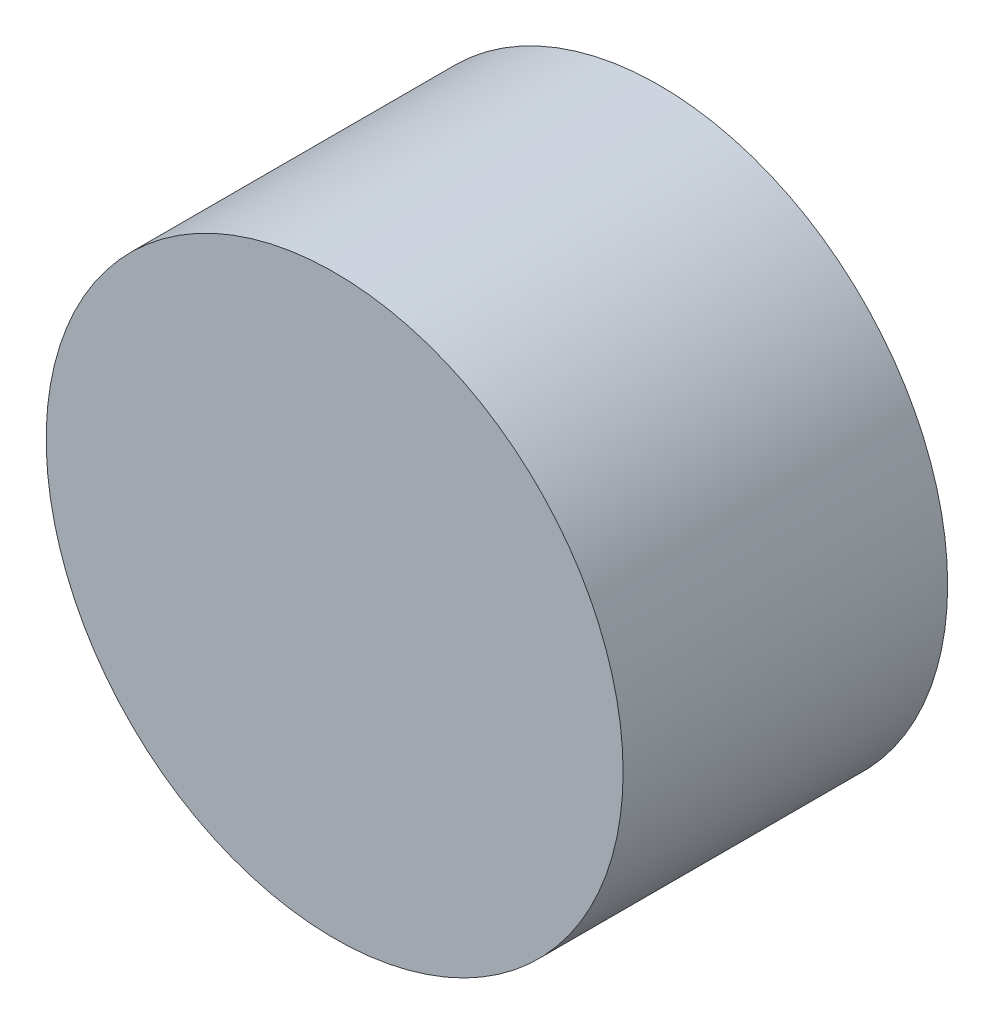
SolidWorks part; units mm, degrees
ref_plane "Płaszczyzna przednia" through (0, 0, 0) normal (0, 0, 1) x (1, 0, 0)
ref_plane "Płaszczyzna górna" through (0, 0, 0) normal (0, 1, 0) x (1, 0, 0)
ref_plane "Płaszczyzna prawa" through (0, 0, 0) normal (1, 0, 0) x (0, 0, -1)
sketch "Szkic1" plane through (0, 0, 0) normal (0, 0, 1) x (1, 0, 0)
  circle A1 centre (0, 0) radius 80
extrude "Dodanie-wyciągnięcie1" add sketch "Szkic1" against normal blind 90
